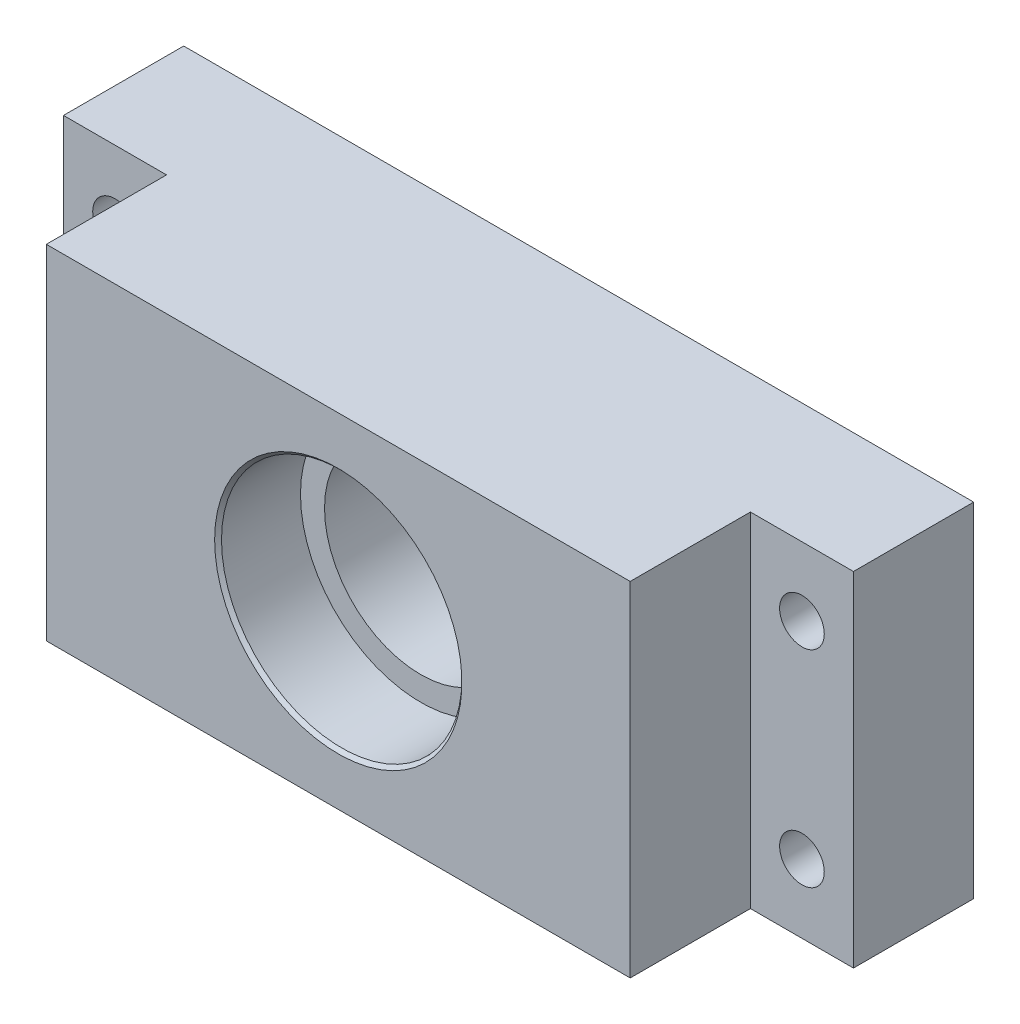
SolidWorks part; units mm, degrees
ref_plane "Płaszczyzna przednia" through (0, 0, 0) normal (0, 0, 1) x (1, 0, 0)
ref_plane "Płaszczyzna górna" through (0, 0, 0) normal (0, 1, 0) x (1, 0, 0)
ref_plane "Płaszczyzna prawa" through (0, 0, 0) normal (1, 0, 0) x (0, 0, -1)
sketch "Szkic1" plane through (0, 0, 0) normal (0, 0, 1) x (1, 0, 0)
  line L1 (-57.5, -25) -> (57.5, -25)
  line L2 (-57.5, -25) -> (-57.5, 25)
  line L3 (-57.5, 25) -> (57.5, 25)
  line L4 (57.5, -25) -> (57.5, 25)
  line L5 (-57.5, -25) -> (57.5, 25) construction
  line L6 (-57.5, 25) -> (57.5, -25) construction
  circle A0 centre (0, 0) radius 14
  point P0 (0, 0)
  dimension "D1" = 28
  dimension "D2" = 115
  dimension "D3" = 50
extrude "Dodanie-wyciągnięcie1" add sketch "Szkic1" along normal blind 35
sketch "Szkic2" plane through (0, 0, 35) normal (0, 0, 1) x (1, 0, 0)
  circle A0 centre (0, 0) radius 17.5
extrude "Wytnij-wyciągnięcie1" cut sketch "Szkic2" against normal blind 12
sketch "Szkic3" plane through (0, 0, 0) normal (0, 0, -1) x (-1, 0, 0)
  circle A0 centre (0, 0) radius 17.5
extrude "Wytnij-wyciągnięcie2" cut sketch "Szkic3" against normal blind 12
sketch "Szkic4" plane through (0, 0, 0) normal (0, 0, -1) x (-1, 0, 0)
  line L0 (-57.5, -25) -> (-57.5, 25) construction
  line L1 (-50, -15) -> (50, -15) construction
  line L2 (-50, -15) -> (-50, 15) construction
  line L3 (-50, 15) -> (50, 15) construction
  line L4 (50, -15) -> (50, 15) construction
  line L5 (-50, -15) -> (50, 15) construction
  line L6 (-50, 15) -> (50, -15) construction
  line L7 (-57.5, 25) -> (57.5, 25) construction
  circle A0 centre (-50, 15) radius 3.25
  circle A1 centre (-50, -15) radius 3.25
  circle A2 centre (50, 15) radius 3.25
  circle A3 centre (50, -15) radius 3.25
  point P0 (0, 0)
  dimension "D1" = 6.5
  dimension "D2" = 7.5
  dimension "D3" = 10
extrude "Wytnij-wyciągnięcie3" cut sketch "Szkic4" against normal through all
sketch "Szkic5" plane through (0, 0, 35) normal (0, 0, 1) x (1, 0, 0)
  line L0 (57.5, 25) -> (-57.5, 25) construction
  line L1 (57.5, -25) -> (42.5, -25)
  line L2 (57.5, -25) -> (57.5, 25)
  line L3 (57.5, 25) -> (42.5, 25)
  line L4 (42.5, -25) -> (42.5, 25)
  line L6 (-57.5, -25) -> (-42.5, -25)
  line L7 (-57.5, -25) -> (-57.5, 25)
  line L8 (-57.5, 25) -> (-42.5, 25)
  line L9 (-42.5, -25) -> (-42.5, 25)
  dimension "D1" = 15
  dimension "D2" = 15
extrude "Wytnij-wyciągnięcie4" cut sketch "Szkic5" against normal blind 17.5
chamfer "Sfazowanie1" distance 0.5 angle 45 2 edges at (17.5, 0, 35) (-17.5, 0, 0)
